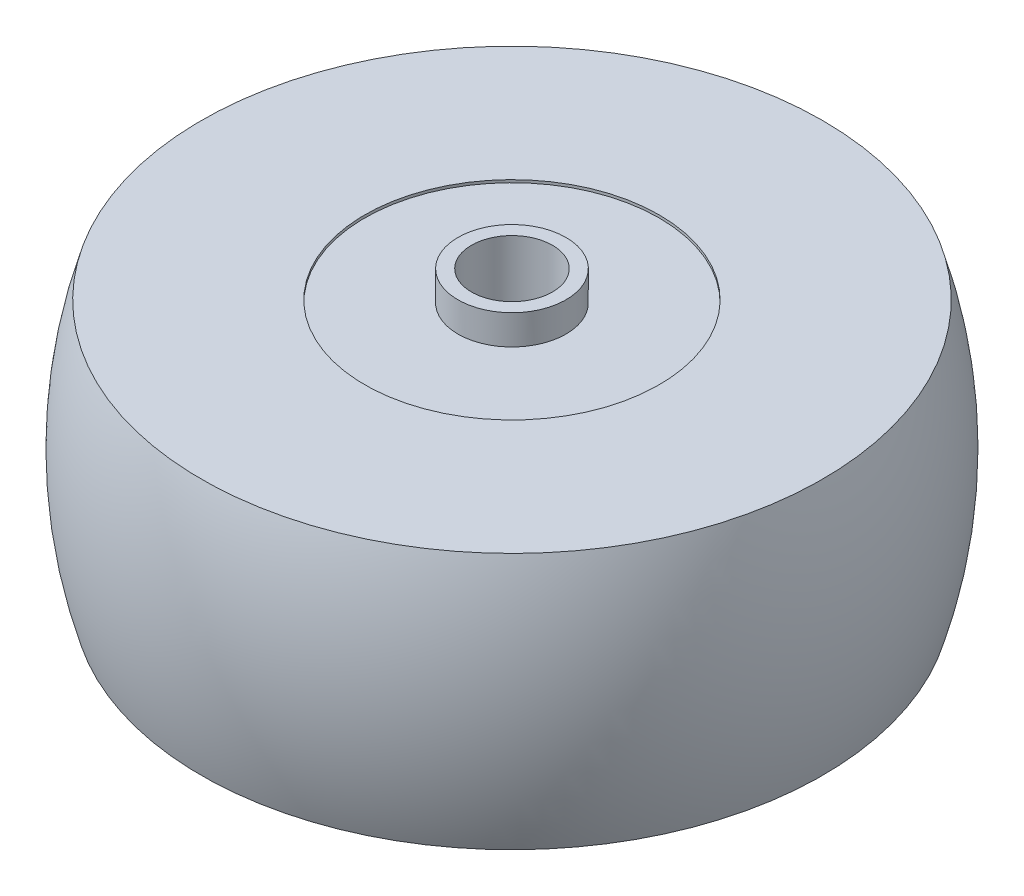
SolidWorks part; units mm, degrees
material "ABS"
ref_plane "Front Plane" through (0, 0, 0) normal (0, 0, 1) x (1, 0, 0)
ref_plane "Top Plane" through (0, 0, 0) normal (0, 1, 0) x (1, 0, 0)
ref_plane "Right Plane" through (0, 0, 0) normal (1, 0, 0) x (0, 0, -1)
sketch "Sketch1" plane through (0, 0, 0) normal (1, 0, 0) x (0, 0, -1)
  line L0 (0, 0) -> (0, 13.5298) construction
  line L1 (3, -9.3) -> (3, 9.3)
  line L2 (3, 9.3) -> (10.9, 9.3)
  line L3 (10.9, 9.3) -> (10.9, 9.5)
  line L4 (10.9, 9.5) -> (23, 9.5)
  line L6 (23, -9.5) -> (10.9, -9.5)
  line L7 (3, -9.3) -> (10.9, -9.3)
  line L8 (10.9, -9.3) -> (10.9, -9.5)
  line L9 (23, 9.5) -> (23, -9.5) construction
  arc A0 (23, 9.5) -> (23, -9.5) centre (-8.5321, 0) cw
  point P3 (3, 0)
  point P11 (23, 0)
  point P12 (24.4, 0)
  dimension "D1" = 48.8
  dimension "D2" = 6
  dimension "D3" = 18.6
  dimension "D4" = 19
  dimension "D5" = 21.8
  dimension "D6" = 23
revolve "Revolve1" add sketch "Sketch1" angle 360 about L0
sketch "Sketch2" plane through (0, 0, 0) normal (0, 0, 1) x (1, 0, 0)
  line L0 (3, 9.3) -> (3, 11.5)
  line L1 (3, 11.5) -> (4, 11.5)
  line L2 (4, 11.5) -> (4, 9.3)
  line L3 (10.9, 9.3) -> (-10.9, 9.3) construction
  line L4 (4, 9.3) -> (3, 9.3)
  line L5 (0, 0) -> (0, 16.5642) construction
  line L6 (3, -9.3) -> (4, -9.3)
  line L7 (3, -9.3) -> (3, -11.5)
  line L8 (3, -11.5) -> (4, -11.5)
  line L9 (4, -9.3) -> (4, -11.5)
  dimension "D1" = 23
  dimension "D2" = 8
revolve "Revolve2" add sketch "Sketch2" angle 360 about L5
